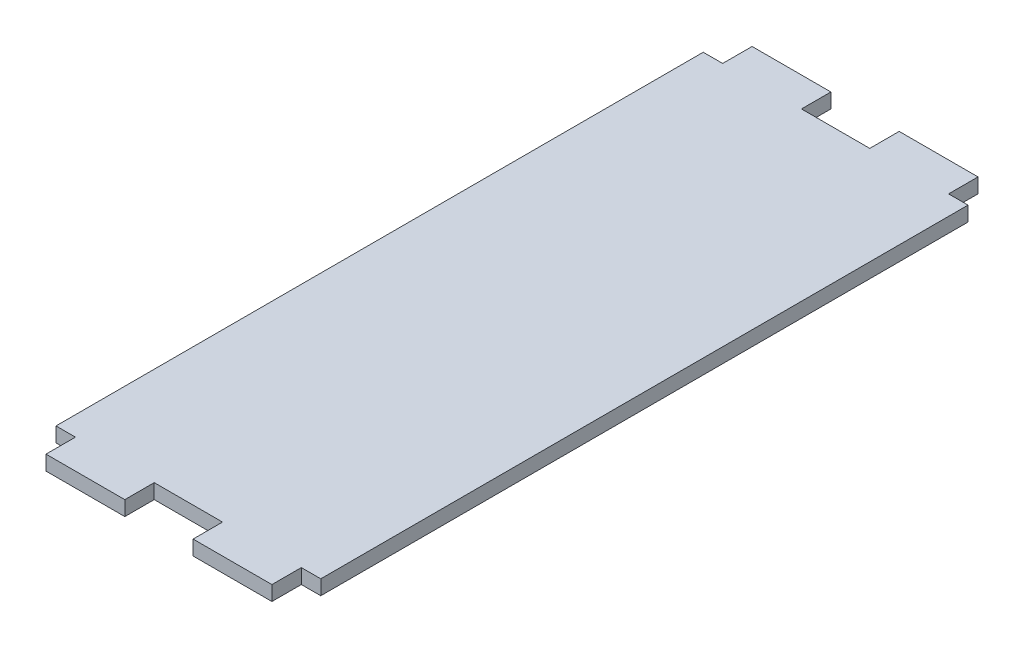
SolidWorks part; units mm, degrees
material "Cedar"
ref_plane "Front Plane" through (0, 0, 0) normal (0, 0, 1) x (1, 0, 0)
ref_plane "Top Plane" through (0, 0, 0) normal (0, 1, 0) x (1, 0, 0)
ref_plane "Right Plane" through (0, 0, 0) normal (1, 0, 0) x (0, 0, -1)
sketch "Sketch1" plane through (0, 0, 0) normal (0, 1, 0) x (1, 0, 0)
  line L1 (-28.575, 76.2) -> (28.575, 76.2)
  line L2 (-28.575, 76.2) -> (-28.575, -76.2)
  line L3 (-28.575, -76.2) -> (28.575, -76.2)
  line L4 (28.575, 76.2) -> (28.575, -76.2)
  line L5 (-28.575, 76.2) -> (28.575, -76.2) construction
  line L6 (-28.575, -76.2) -> (28.575, 76.2) construction
  point P0 (0, 0)
  dimension "D1" = 57.15
  dimension "D2" = 152.4
extrude "Boss-Extrude1" add sketch "Sketch1" along normal blind 3.175
sketch "Sketch2" plane through (0, 3.175, 0) normal (0, 1, 0) x (1, 0, 0)
  line L0 (-28.575, -69.85) -> (28.575, -69.85) construction
  line L1 (-28.575, 76.2) -> (-28.575, -76.2) construction
  line L2 (28.575, -76.2) -> (28.575, 76.2) construction
  line L3 (0, -76.2) -> (0, -69.85) construction
  line L4 (-28.575, -76.2) -> (28.575, -76.2) construction
  line L5 (-24.38, -69.85) -> (-28.575, -69.85)
  line L6 (-24.38, -69.85) -> (-7.37, -69.85) construction
  line L7 (-24.38, -69.85) -> (-24.38, -76.2)
  line L8 (-24.38, -76.2) -> (-7.37, -76.2) construction
  line L9 (-7.37, -69.85) -> (-7.37, -76.2)
  line L10 (-24.38, -69.85) -> (-7.37, -76.2) construction
  line L11 (-24.38, -76.2) -> (-7.37, -69.85) construction
  line L12 (-28.575, -69.85) -> (-28.575, -76.2)
  line L13 (-28.575, -76.2) -> (-24.38, -76.2)
  line L14 (-7.37, -76.2) -> (7.37, -76.2)
  line L15 (0, -76.2) -> (0, -69.85)
  line L16 (7.37, -69.85) -> (-7.37, -69.85)
  line L17 (24.38, -76.2) -> (7.37, -69.85) construction
  line L18 (24.38, -69.85) -> (7.37, -76.2) construction
  line L19 (24.38, -76.2) -> (7.37, -76.2) construction
  line L20 (24.38, -69.85) -> (7.37, -69.85) construction
  line L21 (28.575, -76.2) -> (24.38, -76.2)
  line L22 (28.575, -69.85) -> (28.575, -76.2)
  line L23 (7.37, -69.85) -> (7.37, -76.2)
  line L24 (24.38, -69.85) -> (24.38, -76.2)
  line L25 (24.38, -69.85) -> (28.575, -69.85)
  point P10 (-15.875, -73.025)
  point P22 (15.875, -73.025)
  line M12 (28.575, -76.2) -> (28.575, 76.2)
  line M14 (-28.575, 76.2) -> (-28.575, -76.2)
  line M15 (-28.575, -76.2) -> (28.575, -76.2)
  dimension "D1" = 6.35
  dimension "D2" = 7.37
  dimension "D3" = 17.01
extrude "Cut-Extrude1" cut sketch "Sketch2" against normal through all contours L7 L5 M14 M15 | L15 L16 L9 M15 | L23 L16 L15 L14 | L25 L24 M15 M12
mirror "Mirror1" about plane through (0, 0, 0) normal (0, 0, 1) of "Cut-Extrude1"
